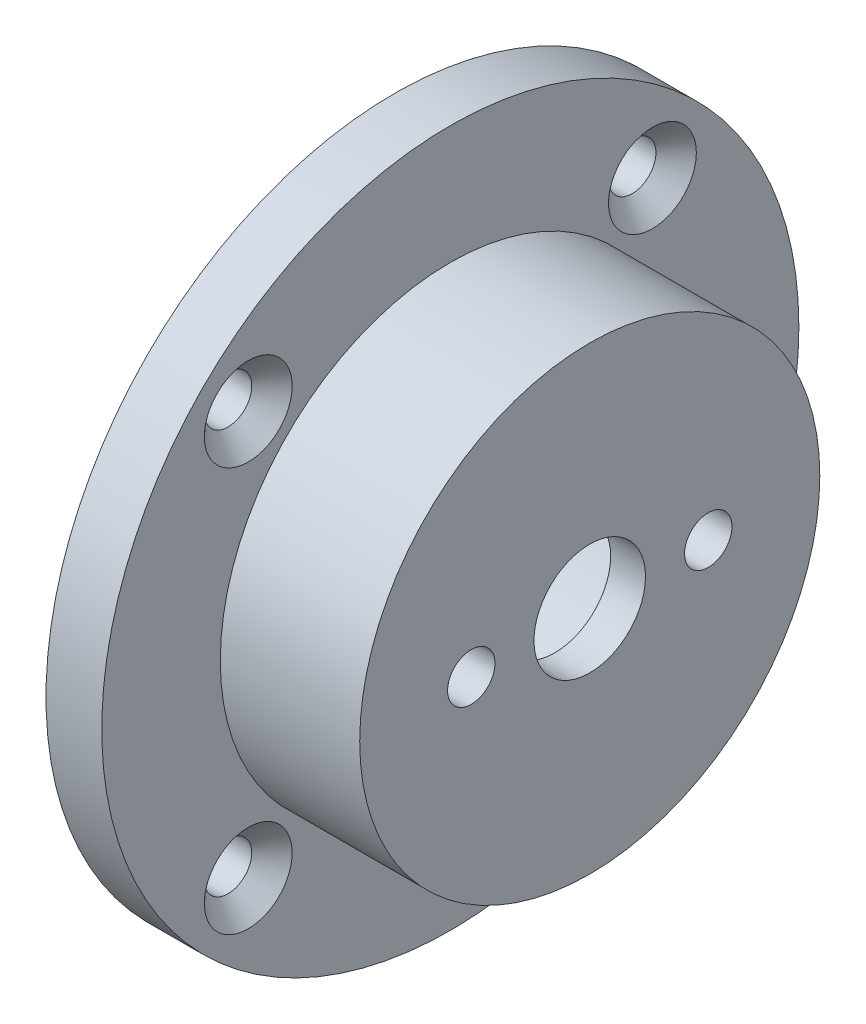
SolidWorks part; units mm, degrees
material "ABS"
ref_plane "Front Plane" through (0, 0, 0) normal (0, 0, 1) x (1, 0, 0)
ref_plane "Top Plane" through (0, 0, 0) normal (0, 1, 0) x (1, 0, 0)
ref_plane "Right Plane" through (0, 0, 0) normal (1, 0, 0) x (0, 0, -1)
sketch "Sketch1" plane through (0, 0, 0) normal (1, 0, 0) x (0, 0, -1)
  circle A0 centre (0, 0) radius 25
extrude "Boss-Extrude1" add sketch "Sketch1" along normal blind 4
sketch "Sketch2" plane through (4, 0, 0) normal (1, 0, 0) x (0, 0, -1)
  circle A0 centre (0, 0) radius 16.5
extrude "Boss-Extrude2" add sketch "Sketch2" along normal blind 10
sketch "Sketch3" plane through (0, 0, 0) normal (-1, 0, 0) x (0, 0, 1)
  circle A0 centre (0, 0) radius 12.5
extrude "Cut-Extrude1" cut sketch "Sketch3" against normal offset from surface (11.5 mm away) 2.5 up to face at (14, 0, -16.5)
sketch "Sketch4" plane through (14, 0, 0) normal (1, 0, 0) x (0, 0, -1)
  circle A0 centre (0, 0) radius 4
extrude "Cut-Extrude2" cut sketch "Sketch4" against normal blind 4
hole_wizard "M3 Clearance Hole1" positions "Sketch6" profile "Sketch5" hole size "M3" standard "ANSI Metric"
sketch "Sketch6" plane through (14, 0, 0) normal (1, 0, 0) x (0, 0, -1)
  point P0 (8.5, 0)
  point P2 (-8.5, 0)
  dimension "D1" = 8.5
  dimension "D2" = 8.5
sketch "Sketch5" plane through (14, 0, -8.5) normal (0, 1, 0) x (0, 0, -1)
  line L0 (0, 0) -> (0, 10)
  line L1 (0, 10) -> (1.7, 10)
  line L2 (1.7, 10) -> (1.7, 0)
  line L5 (1.7, 0) -> (0, 0)
  line L10 (0, 10) -> (-1.7, 10) construction
  line L11 (0, -6.35) -> (0, 107.95) construction
  dimension "Hole Dia." = 3.4
  dimension "Hole Depth" = 10
  dimension "Drill Angle" = 180
sketch "Sketch7" plane through (4, 0, 0) normal (1, 0, 0) x (0, 0, -1)
  line L0 (0, 0) -> (-14.4957, -14.4957) construction
hole_wizard "CSK for M3 Flat Head Machine Screw1" positions "Sketch9" profile "Sketch8" countersink size "M3" standard "ANSI Metric" end condition through all
sketch "Sketch9" plane through (4, 0, 0) normal (1, 0, 0) x (0, 0, -1)
  point P0 (-14.4957, -14.4957)
sketch "Sketch8" plane through (4, -14.4957, 14.4957) normal (0, 1, 0) x (0, 0, -1)
  line L0 (0, 0) -> (0, 4)
  line L1 (0, 4) -> (1.7, 4)
  line L2 (1.7, 4) -> (1.7, 1.45)
  line L3 (1.7, 1.45) -> (3.15, 0)
  line L5 (3.15, 0) -> (0, 0)
  line L6 (-1.7, 1.45) -> (-3.15, 0) construction
  line L11 (0, -6.35) -> (0, 107.95) construction
  dimension "Thru Hole Dia." = 3.4
  dimension "Thru Hole Depth" = 4
  dimension "Near C'Sink Dia." = 6.3
  dimension "Near C'Sink Angle" = 90
pattern_circular "CirPattern1" count 4 over 360 about axis through (0, 0, 0) along (1, 0, 0) of "CSK for M3 Flat Head Machine Screw1"
sketch "Sketch10" plane through (0, 0, 0) normal (-1, 0, 0) x (0, 0, 1)
  circle A0 centre (0, 0) radius 13.125
extrude "Cut-Extrude3" cut sketch "Sketch10" against normal up to surface (11.5 mm away) up to face at (11.5, 0, -10.2)
